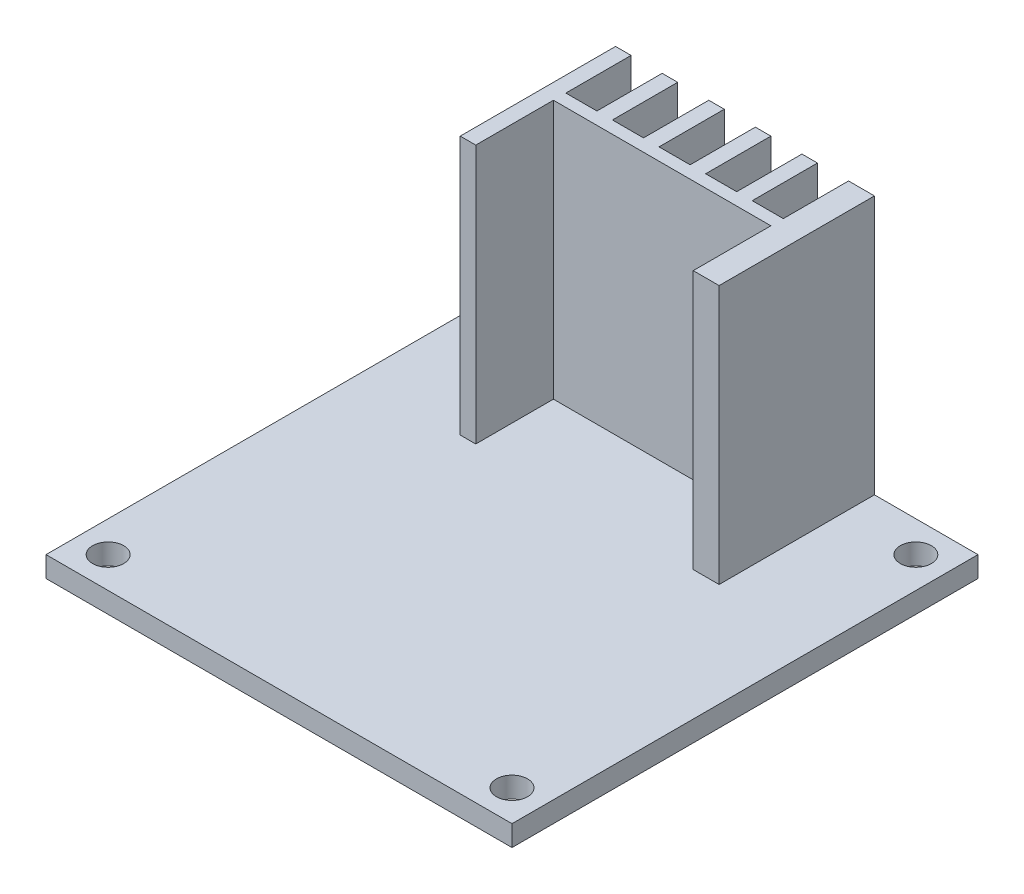
SolidWorks part; units mm, degrees
ref_plane "Front Plane" through (0, 0, 0) normal (0, 0, 1) x (1, 0, 0)
ref_plane "Top Plane" through (0, 0, 0) normal (0, 1, 0) x (1, 0, 0)
ref_plane "Right Plane" through (0, 0, 0) normal (1, 0, 0) x (0, 0, -1)
sketch "Sketch1" plane through (0, 0, 0) normal (0, 1, 0) x (1, 0, 0)
  line L1 (22.5, -22.5) -> (-22.5, -22.5)
  line L2 (22.5, -22.5) -> (22.5, 22.5)
  line L3 (22.5, 22.5) -> (-22.5, 22.5)
  line L4 (-22.5, -22.5) -> (-22.5, 22.5)
  line L5 (22.5, -22.5) -> (-22.5, 22.5) construction
  line L6 (22.5, 22.5) -> (-22.5, -22.5) construction
  circle A0 centre (-19.5, 19.5) radius 1.5
  circle A1 centre (19.5, 19.5) radius 1.5
  circle A2 centre (-19.5, -19.5) radius 1.5
  circle A3 centre (19.5, -19.5) radius 1.5
  point P0 (0, 0)
  dimension "D3" = 3
  dimension "D5" = 3
  dimension "D6" = 3
  dimension "D7" = 3
  dimension "D1" = 45
  dimension "D2" = 45
  dimension "D4" = 3
extrude "Boss-Extrude1" add sketch "Sketch1" along normal blind 2
sketch "Sketch2" plane through (0, 2, 0) normal (0, 1, 0) x (1, 0, 0)
  line L0 (22.5, 22.5) -> (-22.5, 22.5) construction
  line L1 (12.5, 7.5) -> (10, 7.5)
  line L2 (12.5, 7.5) -> (12.5, 22.5)
  line L3 (12.5, 22.5) -> (10, 22.5)
  line L4 (-12.5, 7.5) -> (-12.5, 22.5)
  line L5 (12.5, 7.5) -> (-12.5, 22.5) construction
  line L6 (12.5, 22.5) -> (-12.5, 7.5) construction
  line L7 (0, -22.5) -> (0, 22.5) construction
  line L8 (-22.5, -22.5) -> (22.5, -22.5) construction
  line L9 (-12.5, 15) -> (12.5, 15) construction
  line L10 (-11, 22.5) -> (-11, 16.2)
  line L11 (-11, 16.2) -> (-8, 16.2)
  line L12 (-8, 16.2) -> (-8, 22.5)
  line L13 (-8, 22.5) -> (-6.5, 22.5)
  line L14 (-6.5, 22.5) -> (-6.5, 16.2)
  line L15 (-6.5, 16.2) -> (-3.5, 16.2)
  line L16 (-3.5, 16.2) -> (-3.5, 22.5)
  line L17 (-2, 22.5) -> (-2, 16.2)
  line L18 (-2, 16.2) -> (1, 16.2)
  line L19 (1, 16.2) -> (1, 22.5)
  line L20 (1, 22.5) -> (2.5, 22.5)
  line L21 (2.5, 22.5) -> (2.5, 16.2)
  line L22 (2.5, 16.2) -> (5.5, 16.2)
  line L23 (5.5, 16.2) -> (5.5, 22.5)
  line L24 (7, 22.5) -> (7, 16.2)
  line L25 (7, 16.2) -> (10, 16.2)
  line L26 (10, 16.2) -> (10, 22.5)
  line L27 (-11, 7.5) -> (-11, 15)
  line L28 (-11, 15) -> (10, 15)
  line L29 (10, 15) -> (10, 7.5)
  line L30 (-11, 7.5) -> (-12.5, 7.5)
  line L31 (7, 22.5) -> (5.5, 22.5)
  line L32 (2.5, 22.5) -> (1, 22.5)
  line L33 (-2, 22.5) -> (-3.5, 22.5)
  line L34 (-6.5, 22.5) -> (-8, 22.5)
  line L35 (-11, 22.5) -> (-12.5, 22.5)
  point P0 (0, 15)
  line M23 (22.5, 22.5) -> (-22.5, 22.5)
  dimension "D1" = 25
  dimension "D2" = 15
  dimension "D3" = 1.5
  dimension "D4" = 3
  dimension "D5" = 1.5
  dimension "D6" = 3
  dimension "D7" = 1.5
  dimension "D8" = 1.5
  dimension "D9" = 3
  dimension "D10" = 3
  dimension "D11" = 1.5
  dimension "D12" = 1.5
  dimension "D13" = 3
extrude "Boss-Extrude2" add sketch "Sketch2" along normal blind 25 contours L30 L27 L28 L29 L1 L2 L26 L25 L24 L23 L22 L21 L19 L18 L17 L16 L15 L14 L12 L11 L10 L4 M23
sketch "Sketch3" plane through (0, 0, -22.5) normal (0, 0, -1) x (-1, 0, 0)
  line L0 (22.5, 2) -> (-22.5, 2)
split line "Split Line1"
